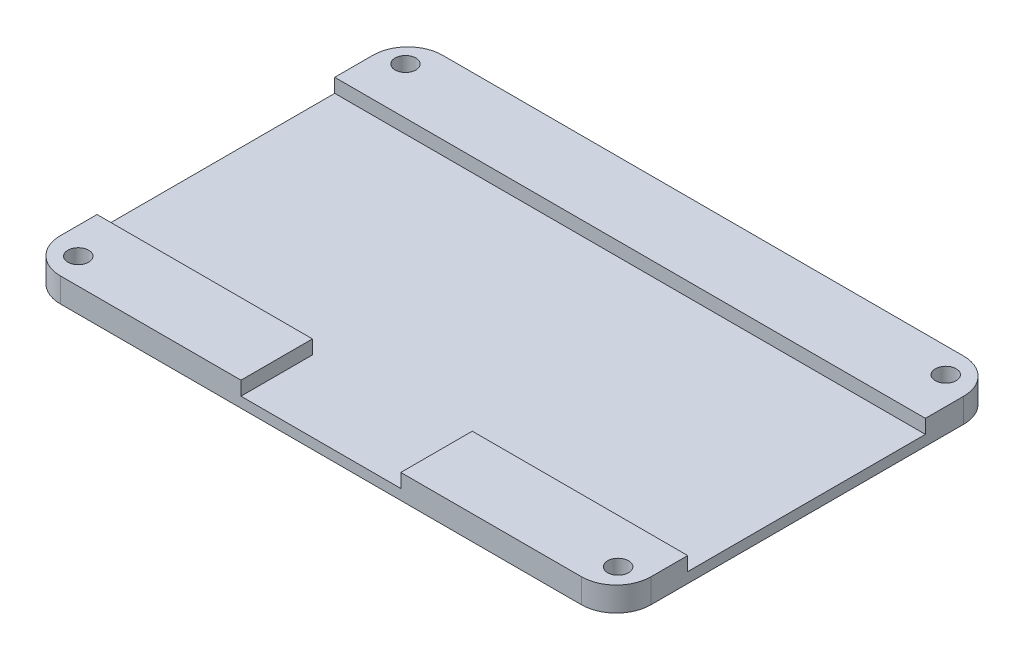
SolidWorks part; units mm, degrees
ref_plane "Front Plane" through (0, 0, 0) normal (0, 0, 1) x (1, 0, 0)
ref_plane "Top Plane" through (0, 0, 0) normal (0, 1, 0) x (1, 0, 0)
ref_plane "Right Plane" through (0, 0, 0) normal (1, 0, 0) x (0, 0, -1)
sketch "Sketch1" plane through (0, 0, 0) normal (0, 1, 0) x (1, 0, 0)
  line L1 (-20.6225, 7.5653) -> (54.3775, 7.5653)
  line L2 (-25.6225, 2.5653) -> (-25.6225, -42.4347)
  line L3 (-20.6225, -47.4347) -> (54.3775, -47.4347)
  line L4 (59.3775, 2.5653) -> (59.3775, -42.4347)
  arc A0 (54.3775, -47.4347) -> (59.3775, -42.4347) centre (54.3775, -42.4347) ccw
  arc A1 (-20.6225, -47.4347) -> (-25.6225, -42.4347) centre (-20.6225, -42.4347) cw
  arc A2 (59.3775, 2.5653) -> (54.3775, 7.5653) centre (54.3775, 2.5653) ccw
  arc A3 (-25.6225, 2.5653) -> (-20.6225, 7.5653) centre (-20.6225, 2.5653) cw
  point P7 (59.3775, -47.4347)
  point P12 (59.3775, 7.5653)
  point P15 (-25.6225, 7.5653)
  dimension "D3" = 5
  dimension "D1" = 85
  dimension "D2" = 55
extrude "Boss-Extrude1" add sketch "Sketch1" along normal blind 3.5
sketch "Sketch2" plane through (0, 3.5, 0) normal (0, 1, 0) x (1, 0, 0)
  circle A0 centre (-22.1876, 3.8027) radius 2.8
  circle A3 centre (-21.7754, -43.6973) radius 2.8
  circle A4 centre (55.4124, 3.9479) radius 2.8
  circle A5 centre (55.7665, -43.5521) radius 2.8
  circle A6 centre (-22.1876, 3.8027) radius 1.5
  circle A7 centre (55.4124, 3.9479) radius 1.5
  circle A8 centre (55.7665, -43.5521) radius 1.5
  circle A9 centre (-21.7754, -43.6973) radius 1.5
  dimension "D1" = 47.5
  dimension "D2" = 47.5
  dimension "D3" = 77.6
extrude "Cut-Extrude1" cut sketch "Sketch2" against normal blind 3.5 contours A9 | A8 | A7 | A6
sketch "Sketch3" plane through (0, 3.5, 0) normal (0, 1, 0) x (1, 0, 0)
  line L0 (-25.6225, 2.5653) -> (-25.6225, -42.4347) construction
  line L1 (-25.6225, -2.9473) -> (59.3775, -2.9473)
  line L2 (-25.6225, -2.9473) -> (-25.6225, -37.151)
  line L3 (-25.6225, -37.151) -> (59.3775, -37.151)
  line L4 (59.3775, -2.9473) -> (59.3775, -37.151)
  line L5 (59.3775, -42.4347) -> (59.3775, 2.5653) construction
  line L6 (5.3775, -37.151) -> (5.3775, -47.4347)
  line L7 (-20.6225, -47.4347) -> (54.3775, -47.4347) construction
  line L8 (5.3775, -47.4347) -> (28.3775, -47.4347)
  line L9 (28.3775, -47.4347) -> (28.3775, -37.151)
  circle A0 centre (-22.1876, 3.8027) radius 1.5 construction
  line M12 (59.3775, -42.4347) -> (59.3775, 2.5653)
  line M16 (-25.6225, 2.5653) -> (-25.6225, -42.4347)
  line M18 (-20.6225, -47.4347) -> (54.3775, -47.4347)
  dimension "D2" = 23
  dimension "D1" = 6.75
  dimension "D3" = 31
extrude "Cut-Extrude2" cut sketch "Sketch3" against normal blind 2 contours L9 L3 L6 M18 | L3 L1 M16 M12
